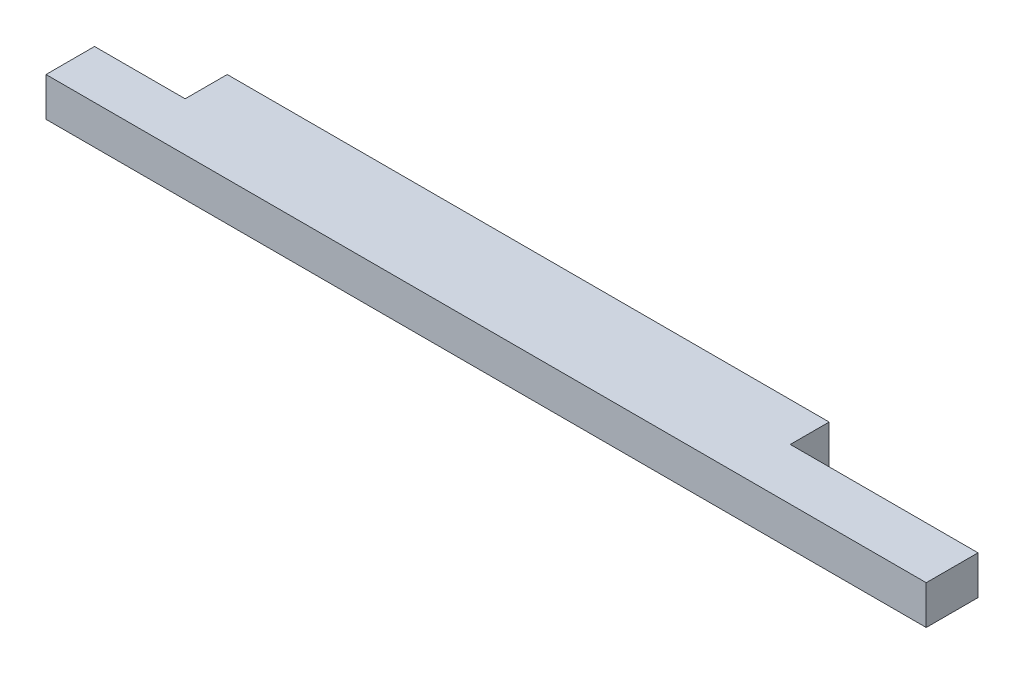
SolidWorks part; units mm, degrees
material "Pine"
ref_plane "Front Plane" through (0, 0, 0) normal (0, 0, 1) x (1, 0, 0)
ref_plane "Top Plane" through (0, 0, 0) normal (0, 1, 0) x (1, 0, 0)
ref_plane "Right Plane" through (0, 0, 0) normal (1, 0, 0) x (0, 0, -1)
sketch "Sketch1" plane through (0, 0, 0) normal (0, 1, 0) x (1, 0, 0)
  line L1 (0, 0) -> (863.6, 0)
  line L2 (0, 0) -> (0, 88.9)
  line L3 (0, 88.9) -> (863.6, 88.9)
  line L4 (863.6, 0) -> (863.6, 88.9)
  dimension "D1" = 88.9
  dimension "D2" = 863.6
extrude "Boss-Extrude1" add sketch "Sketch1" along normal blind 38.1
sketch "Sketch3" plane through (0, 38.1, 0) normal (0, 1, 0) x (1, 0, 0)
  line L5 (863.6, 88.9) -> (679.45, 88.9)
  line L6 (863.6, 88.9) -> (863.6, 50.8)
  line L7 (863.6, 50.8) -> (679.45, 50.8)
  line L8 (679.45, 88.9) -> (679.45, 50.8)
  dimension "D2" = 184.15
  dimension "D4" = 38.1
extrude "Cut-Extrude1" cut sketch "Sketch3" against normal through all
sketch "Sketch4" plane through (0, 38.1, 0) normal (0, 1, 0) x (1, 0, 0)
  line L0 (679.45, 88.9) -> (0, 88.9) construction
  line L1 (0, 88.9) -> (88.9, 88.9)
  line L2 (0, 88.9) -> (0, 47.625)
  line L3 (0, 47.625) -> (88.9, 47.625)
  line L4 (88.9, 88.9) -> (88.9, 47.625)
  dimension "D1" = 41.275
  dimension "D2" = 88.9
extrude "Cut-Extrude2" cut sketch "Sketch4" against normal through all
